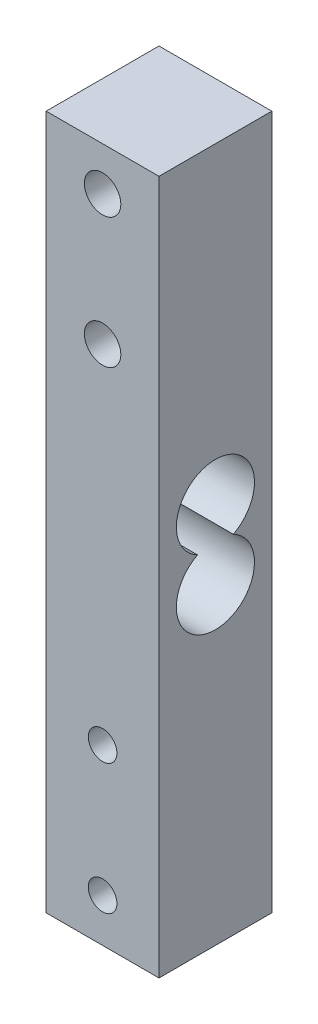
SolidWorks part; units mm, degrees
ref_plane "前视基准面" through (0, 0, 0) normal (0, 0, 1) x (1, 0, 0)
ref_plane "上视基准面" through (0, 0, 0) normal (0, 1, 0) x (1, 0, 0)
ref_plane "右视基准面" through (0, 0, 0) normal (1, 0, 0) x (0, 0, -1)
other "Configuration Table"
sketch "草图1" plane through (0, 0, 0) normal (0, 0, 1) x (1, 0, 0)
  line L1 (-5.9398, 14.2953) -> (7.0602, 14.2953)
  line L2 (-5.9398, 14.2953) -> (-5.9398, -65.7047)
  line L3 (-5.9398, -65.7047) -> (7.0602, -65.7047)
  line L4 (7.0602, 14.2953) -> (7.0602, -65.7047)
  circle A1 centre (0.5602, 9.2953) radius 2.1
  circle A2 centre (0.5602, -5.7047) radius 2.1
  circle A3 centre (0.5602, -60.7047) radius 1.65
  circle A4 centre (0.5602, -45.7047) radius 1.65
  dimension "D3" = 4.2
  dimension "D6" = 15
  dimension "D7" = 4.2
  dimension "D8" = 3.3
  dimension "D9" = 3.3
  dimension "D1" = 13
  dimension "D2" = 80
  dimension "D4" = 5
  dimension "D5" = 6.5
  dimension "D10" = 5
  dimension "D11" = 15
extrude "凸台-拉伸1" add sketch "草图1" along normal blind 13
sketch "草图4" plane through (7.0602, 0, 0) normal (1, 0, 0) x (0, 0, -1)
  line L3 (-13, -65.7047) -> (-13, 14.2953) construction
  line L5 (-13, 14.2953) -> (0, 14.2953) construction
  line L6 (-13, -65.7047) -> (0, -65.7047) construction
  arc A0 (-4.4384, -25.7047) -> (-8.5616, -25.7047) centre (-6.5, -21.7047) ccw
  arc A1 (-8.5616, -25.7047) -> (-4.4384, -25.7047) centre (-6.5, -29.7047) ccw
  dimension "D1" = 36
  dimension "D2" = 9
  dimension "D6" = 9
  dimension "D3" = 36
  dimension "D4" = 6.5
  dimension "D5" = 6.5
extrude "切除-拉伸4" cut sketch "草图4" against normal blind 13
sketch "草图5" plane through (0, -65.7047, 0) normal (0, -1, 0) x (1, 0, 0)
  line L0 (0, 10.3808) -> (-2.7651, 7.0906)
  line L9 (-2.7651, 7.0906) -> (-0.7984, 7.0906)
  line L10 (-0.7984, 7.0906) -> (-0.7984, 1.3817)
  line L11 (-0.7984, 1.3817) -> (0.7975, 1.3817)
  line L12 (0.7975, 1.3817) -> (0.7975, 7.0906)
  line L13 (0.7975, 7.0906) -> (2.9253, 7.0906)
  line L14 (0, 10.3808) -> (2.9253, 7.0906)
  point P2 (2.9253, 7.0906)
extrude "切除-拉伸5" cut sketch "草图5" against normal blind 3
